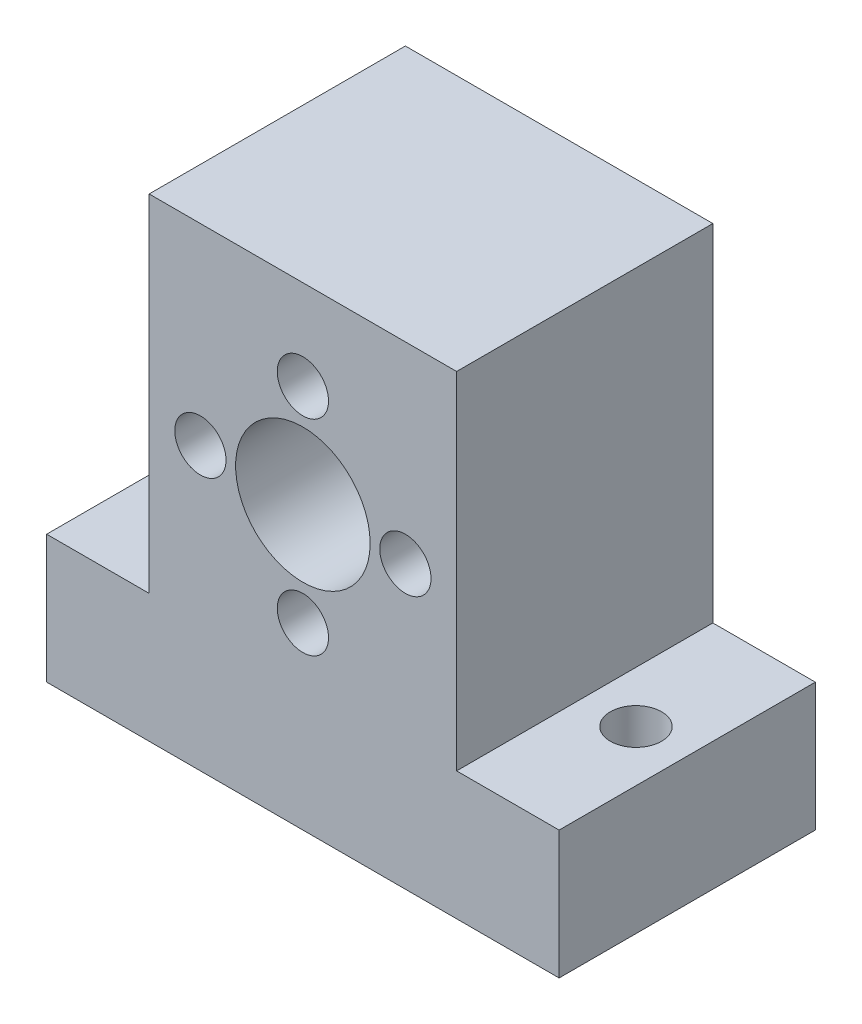
SolidWorks part; units mm, degrees
ref_plane "Front Plane" through (0, 0, 0) normal (0, 0, 1) x (1, 0, 0)
ref_plane "Top Plane" through (0, 0, 0) normal (0, 1, 0) x (1, 0, 0)
ref_plane "Right Plane" through (0, 0, 0) normal (1, 0, 0) x (0, 0, -1)
sketch "Sketch1" plane through (0, 0, 0) normal (0, 0, 1) x (1, 0, 0)
  line L0 (0, -438.3722) -> (0, 21480.2356) construction
  line L1 (-438.3722, 0) -> (21480.2356, 0) construction
  line L3 (-20, -22) -> (20, -22)
  line L4 (-20, -22) -> (-20, 15)
  line L5 (-20, 15) -> (20, 15)
  line L6 (20, -22) -> (20, 15)
  circle A0 centre (0, 0) radius 5.25
  circle A1 centre (0, 0) radius 8 construction
  circle A2 centre (0, 8) radius 2
  circle A3 centre (8, 0) radius 2
  circle A4 centre (0, -8) radius 2
  circle A5 centre (-8, 0) radius 2
  point P4 (0, 0)
  point P24 (0, 0)
  dimension "D2" = 10.5
  dimension "D4" = 16
  dimension "D5" = 4
  dimension "D7" = 8
  dimension "D8" = 8
  dimension "D1" = 15
  dimension "D3" = 40
  dimension "D9" = 22
  dimension "D10" = 20
  dimension "D6" = 4
extrude "Boss-Extrude1" add sketch "Sketch1" along normal blind 20
sketch "Sketch2" plane through (0, 15, 0) normal (0, 1, 0) x (1, 0, 0)
  line L0 (0, -1000) -> (0, 49000) construction
  line L1 (-1030, -10) -> (48970, -10) construction
  line L2 (-20, -20) -> (-20, 0) construction
  circle A0 centre (-16, -10) radius 2
  circle A1 centre (16, -10) radius 2
  point P8 (-20, -10)
  dimension "D2" = 4
  dimension "D1" = 4
extrude "Cut-Extrude1" cut sketch "Sketch2" against normal through all
sketch "Sketch3" plane through (0, 0, 0) normal (0, 0, -1) x (-1, 0, 0)
  line L0 (0, -1000) -> (0, 49000) construction
  line L1 (-1000, 0) -> (49000, 0) construction
  line L2 (-20, 15) -> (20, 15) construction
  line L3 (20, -22) -> (12, -22)
  line L4 (20, -22) -> (20, 15)
  line L5 (20, 15) -> (12, 15)
  line L6 (12, -22) -> (12, 15)
  line L7 (20, -12) -> (12, -12)
  line L8 (-20, -12) -> (-12, -12)
  line L9 (-12, -22) -> (-12, 15)
  line L10 (-20, 15) -> (-12, 15)
  line L11 (-20, -22) -> (-20, 15)
  line L12 (-20, -22) -> (-12, -22)
  line M7 (-20, 15) -> (-20, -22)
  line M10 (20, 15) -> (-20, 15)
  dimension "D1" = 12
  dimension "D2" = 10
extrude "Cut-Extrude2" cut sketch "Sketch3" against normal through all contours L7 L4 L6 M10 | L8 L9 M10 M7
